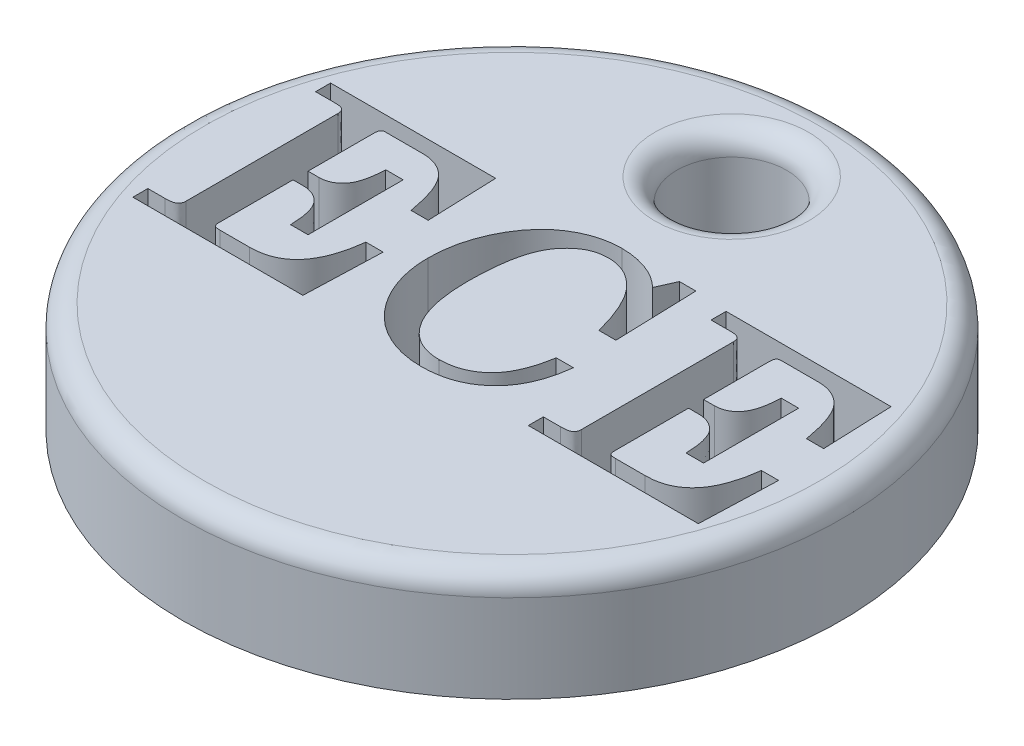
SolidWorks part; units mm, degrees
ref_plane "Front Plane" through (0, 0, 0) normal (0, 0, 1) x (1, 0, 0)
ref_plane "Top Plane" through (0, 0, 0) normal (0, 1, 0) x (1, 0, 0)
ref_plane "Right Plane" through (0, 0, 0) normal (1, 0, 0) x (0, 0, -1)
sketch "Sketch1" plane through (0, 0, 0) normal (0, 1, 0) x (1, 0, 0)
  line L0 (-14.3276, -4.4407) -> (14.3276, -4.4407) construction
  circle A0 centre (0, 0) radius 15
  circle A1 centre (0, 10) radius 2.5
  text T0 "<b>ECE</b>" font "Century" height 9
  point P6 (0, 10.6149)
  dimension "D1" = 30
  dimension "D2" = 5
  dimension "D3" = 10
extrude "Boss-Extrude1" add sketch "Sketch1" along normal blind 4
sketch "Sketch2" plane through (0, 0, 0) normal (0, -1, 0) x (1, 0, 0)
  circle A0 centre (0, 0) radius 15
  circle A1 centre (0, 0) radius 15 construction
  circle A4 centre (0, -10) radius 2.5
  circle A5 centre (0, -10) radius 2.5
  dimension "D1" = 0
extrude "Boss-Extrude2" add sketch "Sketch2" along normal blind 1
fillet "Fillet1" radius 1 2 edges at (0, 4, -7.5) (0, 4, 15)
